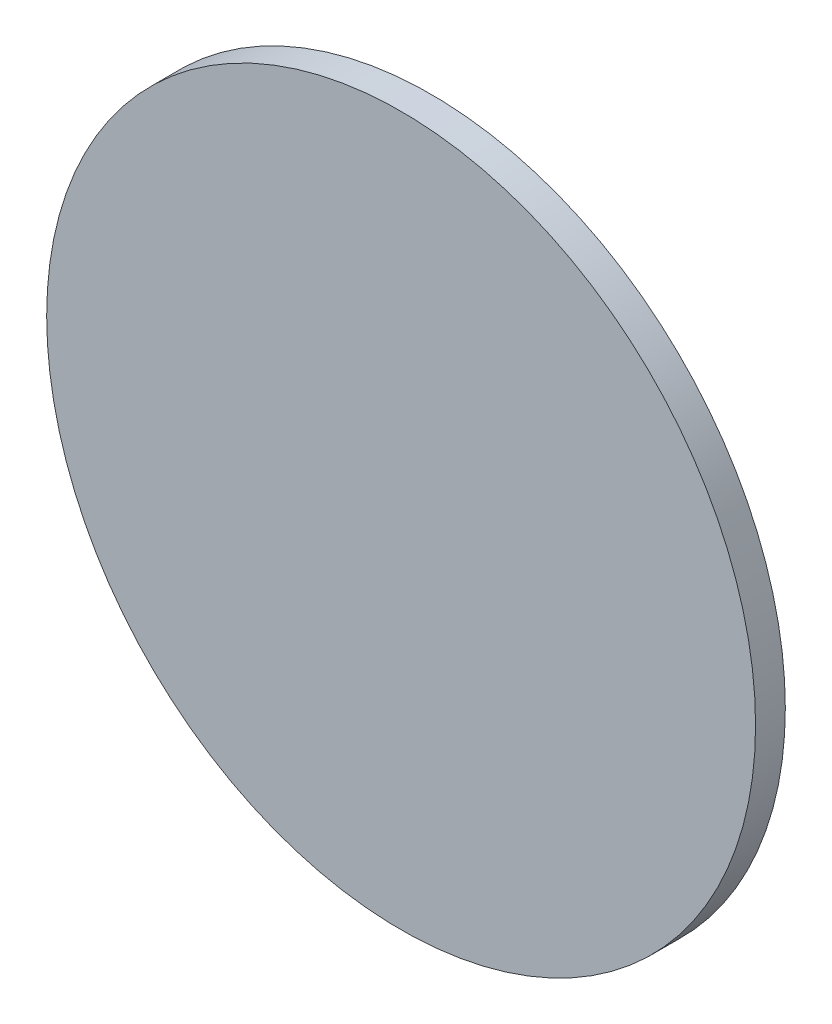
SolidWorks part; units mm, degrees
ref_plane "前视基准面" through (0, 0, 0) normal (0, 0, 1) x (1, 0, 0)
ref_plane "上视基准面" through (0, 0, 0) normal (0, 1, 0) x (1, 0, 0)
ref_plane "右视基准面" through (0, 0, 0) normal (1, 0, 0) x (0, 0, -1)
sketch "草图1" plane through (0, 0, 0) normal (0, 0, 1) x (1, 0, 0)
  circle A0 centre (0, 0) radius 12.5
extrude "凸台-拉伸1" add sketch "草图1" along normal blind 1.05
